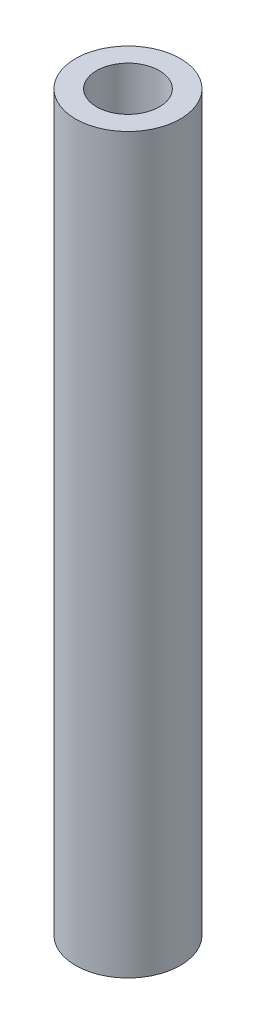
SolidWorks part; units mm, degrees
material "6061 合金"
ref_plane "前视基准面" through (0, 0, 0) normal (0, 0, 1) x (1, 0, 0)
ref_plane "上视基准面" through (0, 0, 0) normal (0, 1, 0) x (1, 0, 0)
ref_plane "右视基准面" through (0, 0, 0) normal (1, 0, 0) x (0, 0, -1)
sketch "草图1" plane through (0, 0, 0) normal (0, 1, 0) x (1, 0, 0)
  circle A0 centre (0, 0) radius 2.5
  circle A1 centre (0, 0) radius 1.5
extrude "凸台-拉伸1" add sketch "草图1" along normal blind 35
